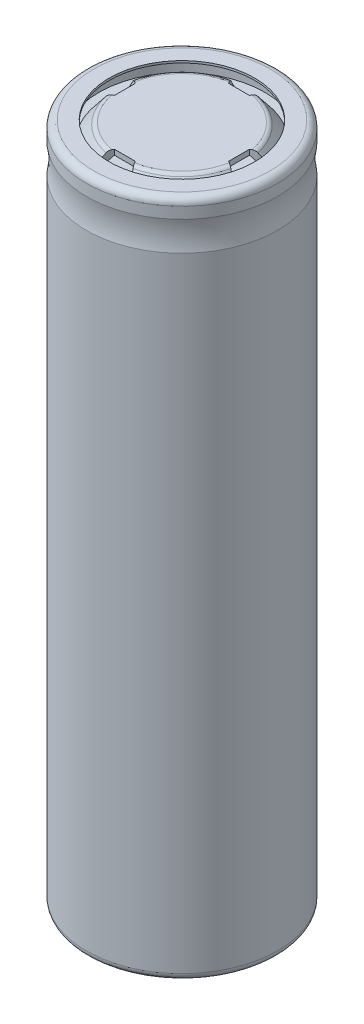
SolidWorks part; units mm, degrees
ref_plane "Спереди" through (0, 0, 0) normal (0, 0, 1) x (1, 0, 0)
ref_plane "Сверху" through (0, 0, 0) normal (0, 1, 0) x (1, 0, 0)
ref_plane "Справа" through (0, 0, 0) normal (1, 0, 0) x (0, 0, -1)
sketch "Эскиз1" plane through (0, 0, 0) normal (0, 0, 1) x (1, 0, 0)
  line L0 (0, 0) -> (0, 113.9204) construction
  line L1 (0, 0) -> (8.5, 0)
  line L2 (9, 0.5) -> (9, 60.5873)
  line L3 (8.5, 60.5873) -> (8.5, 0.5)
  line L4 (8.4985, 65.0015) -> (10.3122, 65.0015) construction
  line L5 (9, 63.4157) -> (9, 64.5)
  line L6 (0, 0) -> (0, 0.5)
  line L7 (0, 0.5) -> (8.5, 0.5)
  line L8 (7.997, 64.5) -> (7.997, 63.5)
  line L9 (8.4985, 63.4152) -> (8.4985, 64.5)
  line L10 (7.997, 63.5) -> (8.4985, 63.5)
  line L11 (8.4985, 65.0015) -> (-1.0683, 65.0015) construction
  line L12 (0, 65) -> (5.7595, 65.0014)
  line L13 (0, 65) -> (0, 64.5)
  line L14 (7.997, 63.5) -> (7.2, 63.5)
  line L15 (7.2, 63.5) -> (6.1502, 64.8136)
  line L16 (0, 64.5) -> (5.6088, 64.5)
  line L17 (7.2, 63.5) -> (7.2, 63)
  line L18 (7.2, 63) -> (8.2, 63)
  line L19 (8.2, 63) -> (8.2, 63.5)
  line L20 (5.6088, 64.5) -> (6.7, 63.5)
  line L21 (7.2, 63.5) -> (0, 63.5)
  line L22 (0, 63.5) -> (0, 63)
  line L23 (0, 63) -> (7.2, 63)
  arc A0 (9, 0.5) -> (8.5, 0) centre (8.5, 0.5) cw
  arc A1 (9, 64.5) -> (7.997, 64.5) centre (8.4985, 64.5) ccw
  arc A2 (8.6667, 62.9443) -> (8.6667, 61.0587) centre (9, 62.0015) ccw
  arc A3 (9, 63.4157) -> (8.6667, 62.9443) centre (8.5, 63.4157) cw
  arc A4 (9, 60.5873) -> (8.6667, 61.0587) centre (8.5, 60.5873) ccw
  arc A5 (8.1657, 62.9439) -> (8.1667, 61.0587) centre (8.5, 62.0015) ccw
  arc A6 (8.1667, 61.0587) -> (8.5, 60.5873) centre (8, 60.5873) cw
  arc A7 (8.4985, 63.4152) -> (8.1657, 62.9439) centre (7.9985, 63.4152) cw
  arc A8 (5.7595, 65.0014) -> (6.1502, 64.8136) centre (5.7596, 64.5014) cw
  point P7 (9, 0)
  point P18 (9, 63.0015)
  point P30 (8.4985, 63.0015)
  point P43 (6, 65.0015)
  dimension "D3" = 0.5
  dimension "D4" = 0.5015
  dimension "D5" = 1
  dimension "D7" = 0.5
  dimension "D8" = 0.5
  dimension "D14" = 1
  dimension "D12" = 0.5
  dimension "D16" = 0.5
  dimension "D24" = 0.5
  dimension "D1" = 18
  dimension "D2" = 64.5
  dimension "D6" = 2
  dimension "D9" = 2.4985
  dimension "D10" = 0.5
  dimension "D11" = 8.5
  dimension "D13" = 1
  dimension "D15" = 2.4985
  dimension "D17" = 0.5
  dimension "D18" = 12
  dimension "D19" = 0.5
  dimension "D20" = 0.5
  dimension "D21" = 1
  dimension "D22" = 0.8
  dimension "D23" = 5.6088
  dimension "D25" = 0.5
  dimension "D26" = 1
revolve "Повернуть1" add sketch "Эскиз1" angle 360 about L0
sketch "Эскиз2" plane through (0, 64.5, 0) normal (0, -1, 0) x (1, 0, 0)
  line L0 (0, -10.6971) -> (0, 9.7635) construction
  line L1 (-14.6111, 0) -> (9.951, 0) construction
  line L2 (-1, -5.4957) -> (1, -5.4957)
  line L3 (1, -5.4957) -> (2, -7.2)
  line L4 (2, -7.2) -> (-2, -7.2)
  line L5 (-1, -5.4957) -> (-2, -7.2)
  line L6 (-5.4957, 1) -> (-5.4957, -1)
  line L7 (-5.4957, -1) -> (-7.2, -2)
  line L8 (-7.2, -2) -> (-7.2, 2)
  line L9 (-5.4957, 1) -> (-7.2, 2)
  line L10 (1, 5.4957) -> (-1, 5.4957)
  line L11 (-1, 5.4957) -> (-2, 7.2)
  line L12 (-2, 7.2) -> (2, 7.2)
  line L13 (1, 5.4957) -> (2, 7.2)
  line L14 (5.4957, -1) -> (5.4957, 1)
  line L15 (5.4957, 1) -> (7.2, 2)
  line L16 (7.2, 2) -> (7.2, -2)
  line L17 (5.4957, -1) -> (7.2, -2)
  point P12 (0, -7.2)
  point P13 (0, -5.4957)
  point P20 (-7.2, 0)
  point P21 (-5.4957, 0)
  point P26 (0, 7.2)
  point P27 (0, 5.4957)
  point P32 (7.2, 0)
  point P33 (5.4957, 0)
  dimension "D1" = 1.7043
  dimension "D2" = 2
  dimension "D3" = 1
  dimension "D5" = 5.4957
  dimension "D4" = 4
extrude "Вырез-Вытянуть1" cut sketch "Эскиз2" along normal up to surface (1 mm away) and the other way through all up to face at (0, 63.5, -7.997)
sketch "Эскиз3" plane through (0, 0, 0) normal (0, 0, 1) x (1, 0, 0)
  line L0 (0, -2.74) -> (0, 74.3076) construction
  line L1 (9, 64.5) -> (9, 63.4157)
  line L2 (8.4977, 0) -> (7, 0)
  line L3 (9, 64.5) -> (9, 63.4157)
  line L4 (9, 60.5873) -> (9, 0.5)
  line L5 (9, 60.5873) -> (9, 0.5)
  line L6 (8.5953, 0.0092) -> (8.4977, 0)
  line L7 (8.5953, 0.0092) -> (8.4977, 0)
  line L8 (8.4977, 0) -> (-8.5, 0)
  line L10 (-9, 0.5) -> (-9, 60.5873)
  line L12 (-9, 63.4157) -> (-9, 64.5)
  line L14 (-8.5941, 64.9923) -> (8.4962, 65.0015)
  line L16 (-8.5, 0) -> (8.5, 0) construction
  line L17 (7, 0) -> (7, -0.2)
  line L18 (7, -0.2) -> (8.5, -0.2)
  line L19 (9.2, 0.5) -> (9.2, 60.5873)
  line L20 (8.4985, 64.5) -> (8.4985, 65.4748) construction
  line L21 (9.2, 63.4163) -> (9.2, 64.5)
  line L22 (9, 0.5) -> (9.2, 0.5) construction
  line L23 (7, 65.0015) -> (8.4962, 65.0015)
  line L24 (8.4985, 65.0015) -> (-8.4985, 65.0015) construction
  line L25 (7, 65.0015) -> (7, 65.2015)
  line L26 (7, 65.2015) -> (8.4985, 65.2015)
  arc A0 (8.6667, 62.9443) -> (9, 63.4157) centre (8.5, 63.4157) ccw
  arc A2 (8.6667, 62.9443) -> (8.6667, 61.0587) centre (9, 62.0015) ccw
  arc A4 (9, 60.5873) -> (8.6667, 61.0587) centre (8.5, 60.5873) ccw
  arc A6 (8.5953, 0.0092) -> (9, 0.5) centre (8.5, 0.5) ccw
  arc A7 (8.5953, 0.0092) -> (9, 0.5) centre (8.5, 0.5) ccw
  arc A8 (-9, 0.5) -> (-8.5, 0) centre (-8.5, 0.5) ccw
  arc A10 (-8.6667, 61.0587) -> (-9, 60.5873) centre (-8.5, 60.5873) ccw
  arc A12 (-8.6667, 61.0587) -> (-8.6667, 62.9443) centre (-9, 62.0015) ccw
  arc A14 (-9, 63.4157) -> (-8.6667, 62.9443) centre (-8.5, 63.4157) ccw
  arc A16 (-8.5941, 64.9923) -> (-9, 64.5) centre (-8.4985, 64.5) ccw
  arc A18 (9, 64.5) -> (8.4962, 65.0015) centre (8.4985, 64.5) ccw
  arc A19 (9, 64.5) -> (8.4962, 65.0015) centre (8.4985, 64.5) ccw
  arc A21 (8.4985, 65.2015) -> (9.2, 64.5) centre (8.4985, 64.5) cw
  arc A22 (8.5, -0.2) -> (9.2, 0.5) centre (8.5, 0.5) ccw
  spline S0 degree 2 poles (9, 63.4157) (8.6971, 61.9443) (9, 60.5873) knots 0 0 0 0.587528 0.587528 0.587528
  spline S1 degree 2 poles (9.2, 63.4163) (8.9014, 61.9539) (9.2, 60.5873) knots 0 0 0 0.679955 0.679955 0.679955
  dimension "D1" = 7
  dimension "D2" = 0.2
  dimension "D5" = 0.2
  dimension "D7" = 64
  dimension "D4" = 64
  dimension "D6" = 7
  dimension "D8" = 0.2
revolve "Повернуть4" add sketch "Эскиз3" angle 360 about L0
equation "\"D8@Эскиз1\"=\"D7@Эскиз1\""
equation "\"D14@Эскиз1\"=\"D5@Эскиз1\""
equation "\"D15@Эскиз1\"=\"D9@Эскиз1\""
equation "\"D12@Эскиз1\"=\"D7@Эскиз1\""
equation "\"D16@Эскиз1\"=\"D7@Эскиз1\""
equation "\"D17@Эскиз1\"=\"D10@Эскиз1\""
equation "\"D7@Эскиз3\"=\"D4@Эскиз3\""
equation "\"D8@Эскиз3\"=\"D5@Эскиз3\""
